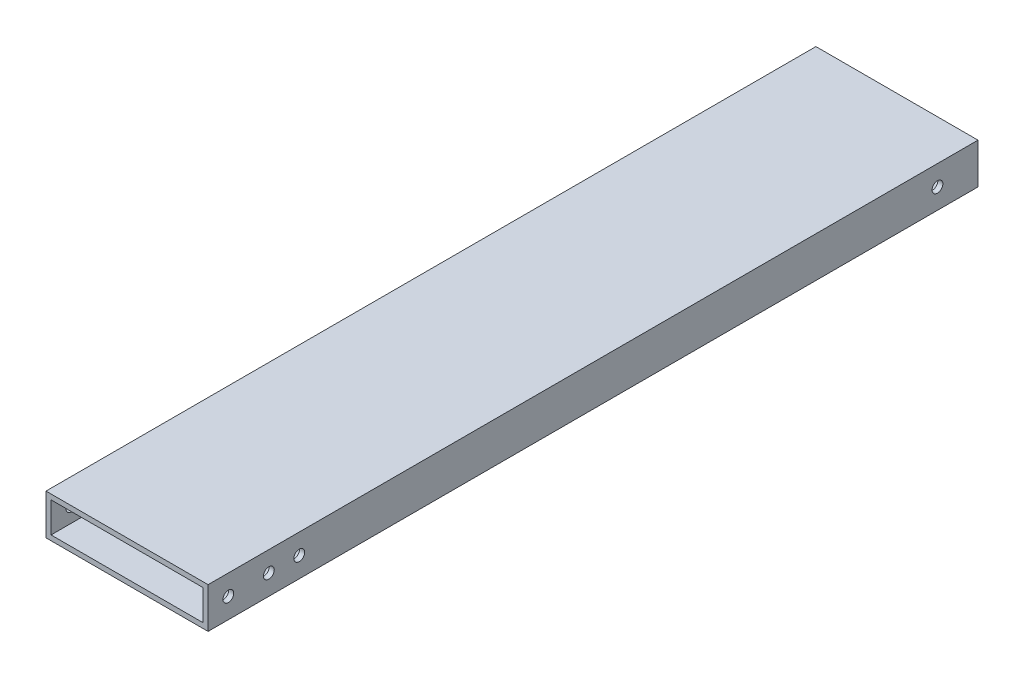
SolidWorks part; units mm, degrees
ref_plane "Front Plane" through (0, 0, 0) normal (0, 0, 1) x (1, 0, 0)
ref_plane "Top Plane" through (0, 0, 0) normal (0, 1, 0) x (1, 0, 0)
ref_plane "Right Plane" through (0, 0, 0) normal (1, 0, 0) x (0, 0, -1)
sketch "Sketch1" plane through (0, 0, 0) normal (0, 0, 1) x (1, 0, 0)
  line L0 (-50.8, 12.7) -> (50.8, 12.7)
  line L1 (-47.625, -9.525) -> (47.625, -9.525)
  line L2 (-47.625, -9.525) -> (-47.625, 9.525)
  line L3 (-47.625, 9.525) -> (47.625, 9.525)
  line L4 (47.625, -9.525) -> (47.625, 9.525)
  line L5 (-47.625, -9.525) -> (47.625, 9.525) construction
  line L6 (-47.625, 9.525) -> (47.625, -9.525) construction
  line L7 (50.8, -12.7) -> (50.8, 12.7)
  line L8 (-50.8, -12.7) -> (50.8, -12.7)
  line L9 (-50.8, -12.7) -> (-50.8, 12.7)
  point P0 (0, 0)
  dimension "D2" = 101.6
  dimension "D3" = 25.4
  dimension "D1" = 3.175
extrude "Boss-Extrude1" add sketch "Sketch1" along normal blind 482.6
hole_wizard "H (0.266) Diameter Hole1" positions "Sketch2" profile "Sketch3" hole size "H" standard "ANSI Inch" end condition through all
sketch "Sketch2" plane through (50.8, 0, 0) normal (1, 0, 0) x (0, 0, -1)
  line L0 (-482.6, -12.7) -> (-482.6, 12.7) construction
  point P0 (-25.4, 0)
  point P2 (-469.9, 0)
  point P4 (-444.5, 0)
  point P6 (-425.45, 0)
  dimension "D1" = 25.4
  dimension "D2" = 12.7
  dimension "D3" = 57.15
  dimension "D4" = 457.2
sketch "Sketch3" plane through (50.8, 0, 25.4) normal (0, 1, 0) x (0, 0, -1)
  line L0 (0, 0) -> (0, 101.6)
  line L1 (0, 101.6) -> (3.3782, 101.6)
  line L2 (3.3782, 101.6) -> (3.3782, 0)
  line L5 (3.3782, 0) -> (0, 0)
  line L11 (0, -6.35) -> (0, 107.95) construction
  dimension "Thru Hole Dia." = 6.7564
  dimension "Thru Hole Depth" = 101.6
